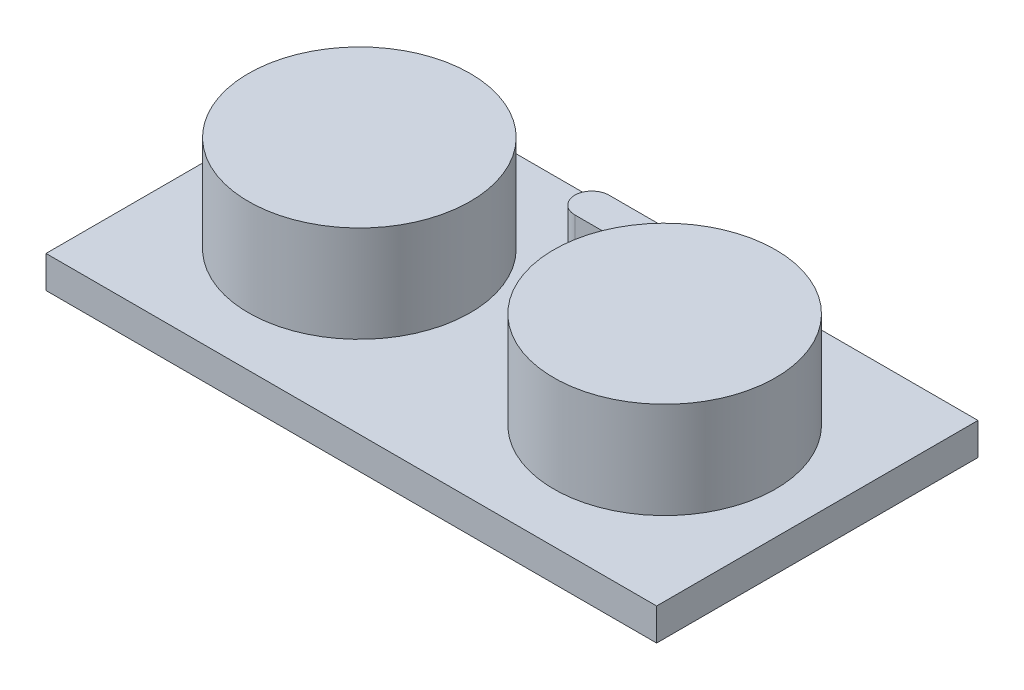
SolidWorks part; units mm, degrees
ref_plane "Front Plane" through (0, 0, 0) normal (0, 0, 1) x (1, 0, 0)
ref_plane "Top Plane" through (0, 0, 0) normal (0, 1, 0) x (1, 0, 0)
ref_plane "Right Plane" through (0, 0, 0) normal (1, 0, 0) x (0, 0, -1)
sketch "Sketch1" plane through (0, 0, 0) normal (0, 1, 0) x (1, 0, 0)
  line L0 (-6.3144, 5.1601) -> (-6.3144, -20.2399)
  line L1 (-30.4444, 5.1601) -> (17.8156, 5.1601)
  line L2 (-30.4444, 5.1601) -> (-30.4444, -20.2399)
  line L3 (-30.4444, -20.2399) -> (17.8156, -20.2399)
  line L4 (17.8156, 5.1601) -> (17.8156, -20.2399)
  circle A0 centre (5.7506, -7.5399) radius 9.1453
  circle A1 centre (-18.3794, -7.5399) radius 9.1453
  dimension "D1" = 48.26
  dimension "D2" = 25.4
extrude "Boss-Extrude1" add sketch "Sketch1" along normal blind 2.54 contours L2 L3 L0 L1 A1 | A0 | L4 L1 L0 L3 A0 | A1
sketch "Sketch4" plane through (0, 2.54, 0) normal (0, 1, 0) x (1, 0, 0)
  line L0 (-6.3144, 5.1601) -> (-6.3144, -20.2399)
  line L1 (-30.4444, 5.1601) -> (17.8156, 5.1601) construction
  line L2 (-30.4444, -20.2399) -> (17.8156, -20.2399) construction
  circle A0 centre (5.7506, -7.5399) radius 8.7652
  circle A1 centre (-18.3794, -7.5399) radius 8.7652
extrude "Boss-Extrude2" add sketch "Sketch4" along normal blind 7.62 contours A1 | A0
sketch "Sketch5" plane through (0, 2.54, 0) normal (0, 1, 0) x (1, 0, 0)
  line L0 (-9.6428, 2.1072) -> (-2.57, 2.1072) construction
  line L1 (-9.6428, 3.4594) -> (-2.57, 3.4594)
  line L2 (-9.6428, 0.7551) -> (-2.57, 0.7551)
  arc A0 (-9.6428, 3.4594) -> (-9.6428, 0.7551) centre (-9.6428, 2.1072) ccw
  arc A1 (-2.57, 0.7551) -> (-2.57, 3.4594) centre (-2.57, 2.1072) ccw
  point P2 (-6.1064, 2.1072)
extrude "Boss-Extrude3" add sketch "Sketch5" along normal blind 5.08 from surface at -2.54 starting at face at (-6.3144, 0, 7.5399)
